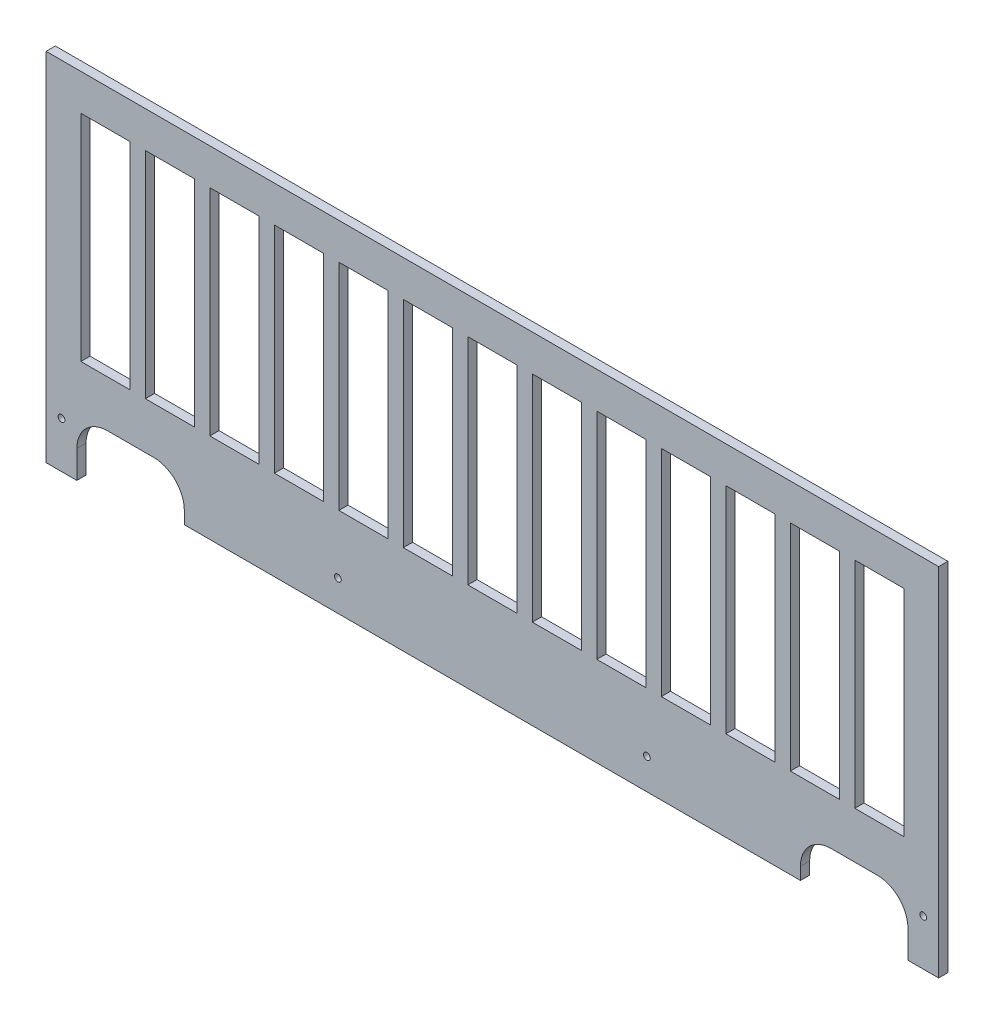
SolidWorks part; units mm, degrees
ref_plane "Plane1" through (0, 0, 0) normal (0, 0, 1) x (1, 0, 0)
ref_plane "Plane2" through (0, 0, 0) normal (0, 1, 0) x (1, 0, 0)
ref_plane "Plane3" through (0, 0, 0) normal (1, 0, 0) x (0, 0, -1)
sketch "Esquisse5" plane through (0, 0, 0) normal (0, 0, 1) x (1, 0, 0)
  line L7 (-3.9285, 116) -> (286.6703, 116)
  line L8 (-3.9285, 116) -> (-3.9285, 0)
  line L9 (16.07, 19.0001) -> (31.07, 19.0001)
  line L10 (286.6703, 116) -> (286.6703, 0)
  line L15 (28.373, 104.2) -> (44.373, 104.2)
  line L16 (7.373, 104.2) -> (23.373, 104.2)
  line L17 (7.373, 104.2) -> (7.373, 34.2)
  line L18 (7.373, 34.2) -> (23.373, 34.2)
  line L19 (23.373, 104.2) -> (23.373, 34.2)
  line L20 (28.373, 104.2) -> (28.373, 34.2)
  line L21 (28.373, 34.2) -> (44.373, 34.2)
  line L22 (44.373, 104.2) -> (44.373, 34.2)
  line L23 (49.373, 104.2) -> (65.373, 104.2)
  line L24 (49.373, 104.2) -> (49.373, 34.2)
  line L25 (49.373, 34.2) -> (65.373, 34.2)
  line L26 (65.373, 104.2) -> (65.373, 34.2)
  line L27 (70.373, 104.2) -> (86.373, 104.2)
  line L28 (70.373, 104.2) -> (70.373, 34.2)
  line L29 (70.373, 34.2) -> (86.373, 34.2)
  line L30 (86.373, 104.2) -> (86.373, 34.2)
  line L31 (91.373, 104.2) -> (107.373, 104.2)
  line L32 (91.373, 104.2) -> (91.373, 34.2)
  line L33 (91.373, 34.2) -> (107.373, 34.2)
  line L34 (107.373, 104.2) -> (107.373, 34.2)
  line L35 (112.373, 104.2) -> (128.373, 104.2)
  line L36 (112.373, 104.2) -> (112.373, 34.2)
  line L37 (112.373, 34.2) -> (128.373, 34.2)
  line L38 (128.373, 104.2) -> (128.373, 34.2)
  line L39 (133.373, 104.2) -> (149.373, 104.2)
  line L40 (133.373, 104.2) -> (133.373, 34.2)
  line L41 (133.373, 34.2) -> (149.373, 34.2)
  line L42 (149.373, 104.2) -> (149.373, 34.2)
  line L43 (154.373, 104.2) -> (170.373, 104.2)
  line L44 (154.373, 104.2) -> (154.373, 34.2)
  line L45 (154.373, 34.2) -> (170.373, 34.2)
  line L46 (170.373, 104.2) -> (170.373, 34.2)
  line L47 (175.373, 104.2) -> (191.373, 104.2)
  line L48 (175.373, 104.2) -> (175.373, 34.2)
  line L49 (175.373, 34.2) -> (191.373, 34.2)
  line L50 (191.373, 104.2) -> (191.373, 34.2)
  line L51 (196.373, 104.2) -> (212.373, 104.2)
  line L52 (196.373, 104.2) -> (196.373, 34.2)
  line L53 (196.373, 34.2) -> (212.373, 34.2)
  line L54 (212.373, 104.2) -> (212.373, 34.2)
  line L55 (217.373, 104.2) -> (233.373, 104.2)
  line L56 (217.373, 104.2) -> (217.373, 34.2)
  line L57 (217.373, 34.2) -> (233.373, 34.2)
  line L58 (233.373, 104.2) -> (233.373, 34.2)
  line L59 (238.373, 104.2) -> (254.373, 104.2)
  line L60 (238.373, 104.2) -> (238.373, 34.2)
  line L61 (238.373, 34.2) -> (254.373, 34.2)
  line L62 (254.373, 104.2) -> (254.373, 34.2)
  line L63 (259.373, 104.2) -> (275.373, 104.2)
  line L64 (259.373, 104.2) -> (259.373, 34.2)
  line L65 (259.373, 34.2) -> (275.373, 34.2)
  line L66 (275.373, 104.2) -> (275.373, 34.2)
  line L71 (-3.9285, 0) -> (6.07, 0)
  line L72 (6.07, 0) -> (6.07, 9.0001)
  line L73 (41.07, 9.0001) -> (41.07, 5.0001)
  line L74 (251.6703, 19.0001) -> (266.6703, 19.0001)
  line L75 (241.6703, 9.0001) -> (241.6703, 5.0001)
  line L77 (276.6703, 0) -> (276.6703, 9)
  line L78 (286.6703, 0) -> (276.6703, 0)
  line L79 (41.07, 5.0001) -> (241.6703, 5.0001)
  circle A0 centre (191.6703, 15) radius 1.1
  arc A1 (16.07, 19.0001) -> (6.07, 9.0001) centre (16.07, 9.0001) ccw
  arc A3 (41.07, 9.0001) -> (31.07, 19.0001) centre (31.07, 9.0001) ccw
  arc A5 (241.6703, 9.0001) -> (251.6703, 19.0001) centre (251.6703, 9.0001) cw
  arc A6 (266.6703, 19.0001) -> (276.6703, 9) centre (266.6703, 9.0001) cw
  circle A7 centre (1.0715, 15) radius 1.1
  circle A8 centre (91.0715, 15) radius 1.1
  circle A9 centre (281.6703, 15) radius 1.1
  point P99 (6.07, 19.0001)
  point P102 (41.07, 19.0001)
  dimension "D3" = 290.5988
  dimension "D12" = 10
  dimension "D15" = 5
  dimension "D16" = 90
  dimension "D17" = 2.2
  dimension "D19" = 10
  dimension "D10" = 15
  dimension "D4" = 3.9285
  dimension "D5" = 9.9985
  dimension "D6" = 14
  dimension "D7" = 19.9985
  dimension "D8" = 35
  dimension "D9" = 35
  dimension "D11" = 116
  dimension "D13" = 5
  dimension "D14" = 90
  dimension "D18" = 15
  dimension "D20" = 200.6003
  dimension "D21" = 15
  dimension "D23" = 11.3015
  dimension "D24" = 16
  dimension "D25" = 5
  dimension "D26" = 70
  dimension "D27" = 11.8
  dimension "D28" = 5.0001
  dimension "D29" = 9
  dimension "D22" = 13
extrude "Extrusion1" add sketch "Esquisse5" along normal blind 3
